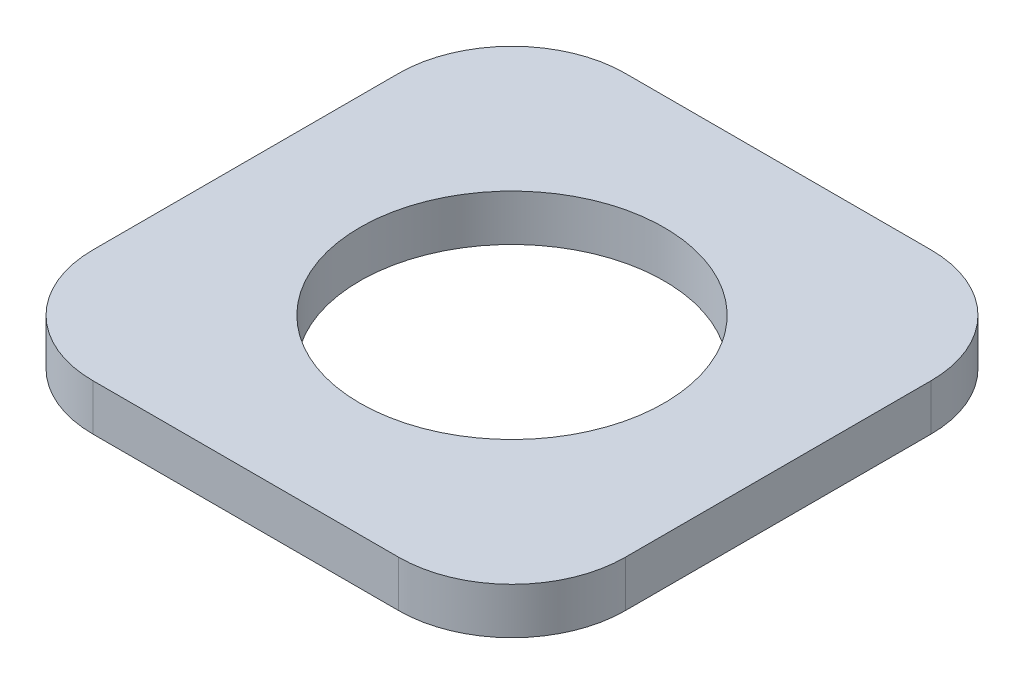
SolidWorks part; units mm, degrees
ref_plane "Alzado" through (0, 0, 0) normal (0, 0, 1) x (1, 0, 0)
ref_plane "Planta" through (0, 0, 0) normal (0, 1, 0) x (1, 0, 0)
ref_plane "Vista lateral" through (0, 0, 0) normal (1, 0, 0) x (0, 0, -1)
sketch "Croquis1" plane through (0, 0, 0) normal (0, 1, 0) x (1, 0, 0)
  line L1 (-46.99, 46.99) -> (46.99, 46.99)
  line L2 (-46.99, 46.99) -> (-46.99, -46.99)
  line L3 (-46.99, -46.99) -> (46.99, -46.99)
  line L4 (46.99, 46.99) -> (46.99, -46.99)
  line L5 (-46.99, 46.99) -> (46.99, -46.99) construction
  line L6 (-46.99, -46.99) -> (46.99, 46.99) construction
  point P0 (0, 0)
  dimension "D1" = 93.98
  dimension "D2" = 93.98
extrude "Saliente-Extruir1" add sketch "Croquis1" along normal blind 8.1661
sketch "Croquis2" plane through (0, 8.1661, 0) normal (0, 1, 0) x (1, 0, 0)
  circle A0 centre (0, 0) radius 26.8605
  dimension "D1" = 53.721
extrude "Cortar-Extruir1" cut sketch "Croquis2" against normal blind 8.1661
fillet "Redondeo1" radius 20 4 edges at (-46.99, 4.0831, 46.99) (46.99, 4.0831, 46.99) (46.99, 4.0831, -46.99) (-46.99, 4.0831, -46.99)
